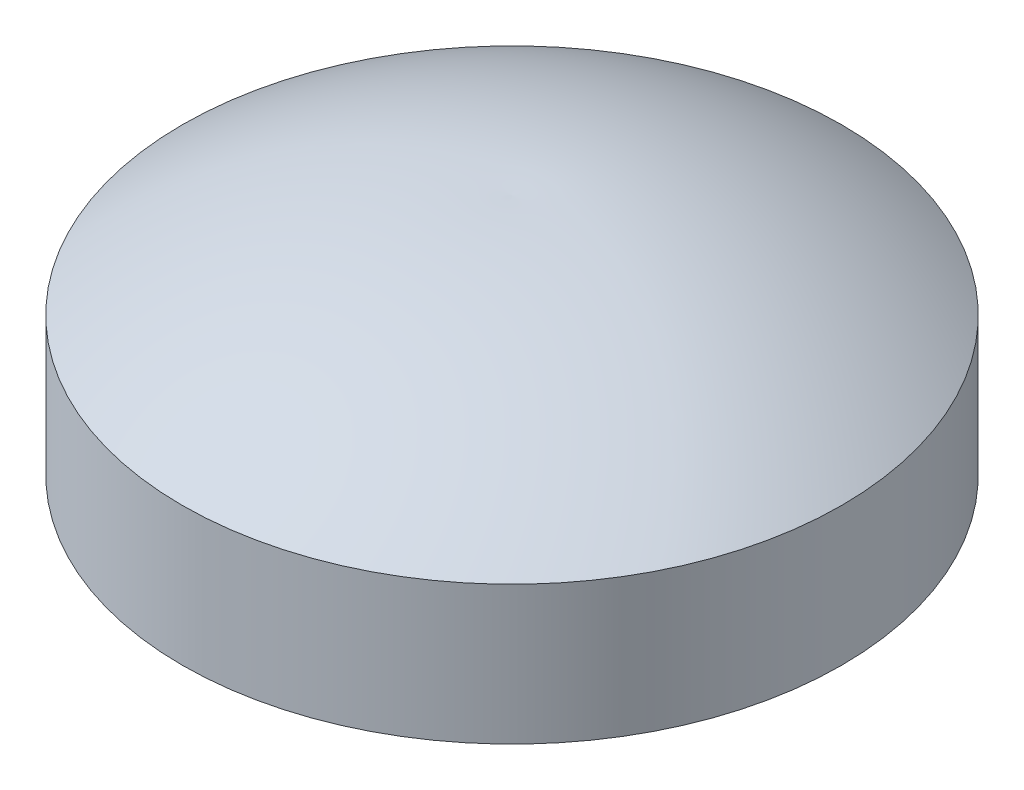
SolidWorks part; units mm, degrees
ref_plane "Front Plane" through (0, 0, 0) normal (0, 0, 1) x (1, 0, 0)
ref_plane "Top Plane" through (0, 0, 0) normal (0, 1, 0) x (1, 0, 0)
ref_plane "Right Plane" through (0, 0, 0) normal (1, 0, 0) x (0, 0, -1)
sketch "Sketch1" plane through (0, 0, 0) normal (0, 0, 1) x (1, 0, 0)
  line L0 (0, 0) -> (4.7625, 0)
  line L1 (4.7625, 0) -> (4.7625, 2)
  line L2 (0, 0) -> (0, 3.5)
  line L3 (4.7625, 2) -> (0, 2) construction
  line L4 (0, 2) -> (-4.7625, 2) construction
  line L5 (-4.7625, 2) -> (-4.7625, 0) construction
  line L6 (-4.7625, 0) -> (0, 0) construction
  line L7 (9.3449, -1.2087) -> (0.1801, 5.2087) construction
  spline S0 degree 2 poles (0, 3.5) (2.4713, 3.6043) (4.7625, 2) knots 0 0 0 1 1 1
  dimension "D4" = 35
  dimension "D1" = 9.525
  dimension "D2" = 2
  dimension "D3" = 3.5
revolve "Revolve1" add sketch "Sketch1" angle 360 about L2
